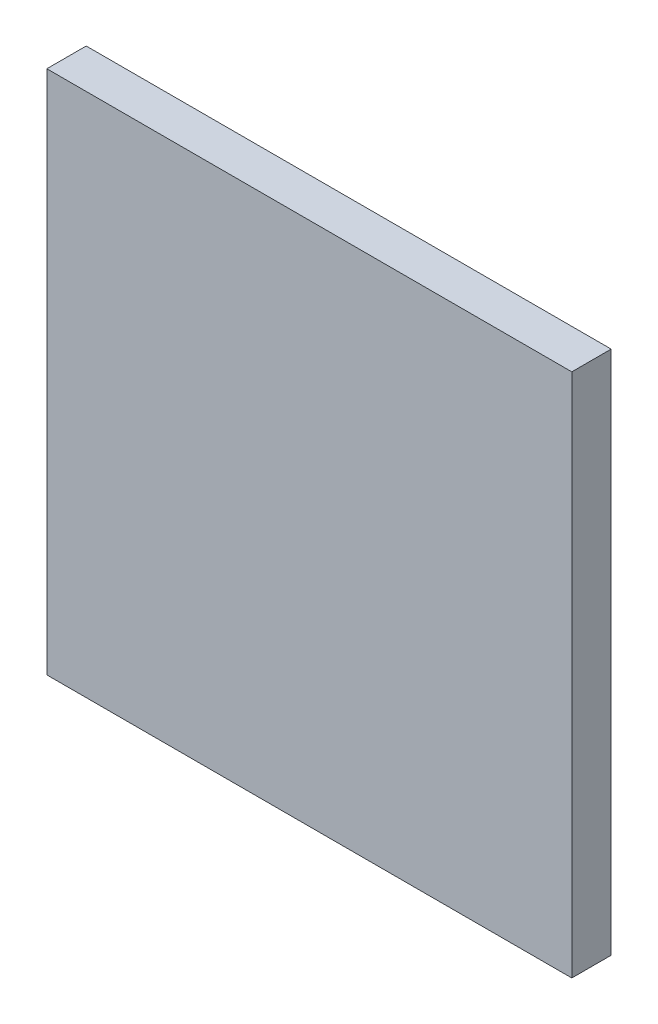
SolidWorks part; units mm, degrees
material "Stainless Steel (ferritic)"
ref_plane "Front Plane" through (0, 0, 0) normal (0, 0, 1) x (1, 0, 0)
ref_plane "Top Plane" through (0, 0, 0) normal (0, 1, 0) x (1, 0, 0)
ref_plane "Right Plane" through (0, 0, 0) normal (1, 0, 0) x (0, 0, -1)
sketch "Sketch1" plane through (0, 0, 0) normal (0, 0, 1) x (1, 0, 0)
  line L1 (-20, -20) -> (20, -20)
  line L2 (-20, -20) -> (-20, 20)
  line L3 (-20, 20) -> (20, 20)
  line L4 (20, -20) -> (20, 20)
  line L5 (-20, -20) -> (20, 20) construction
  line L6 (-20, 20) -> (20, -20) construction
  point P0 (0, 0)
  dimension "D1" = 40
  dimension "D2" = 40
extrude "Boss-Extrude1" add sketch "Sketch1" along normal blind 3
